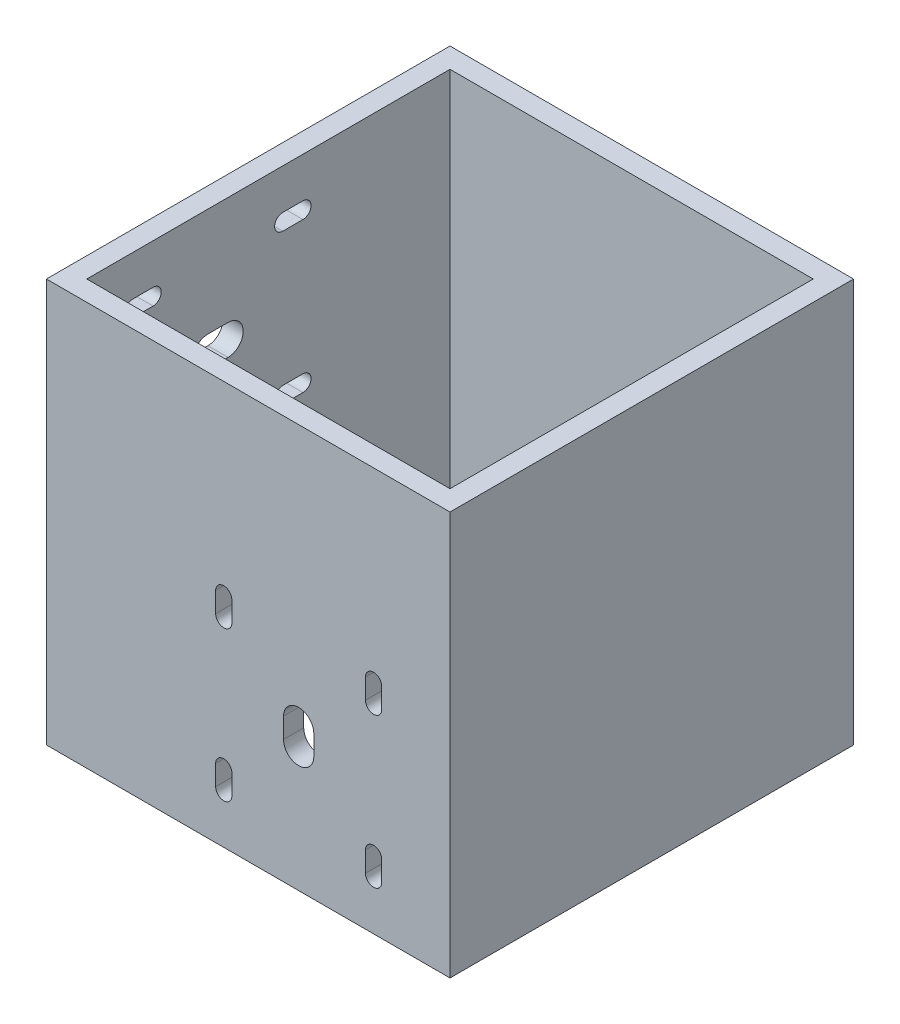
SolidWorks part; units mm, degrees
ref_plane "Front Plane" through (0, 0, 0) normal (0, 0, 1) x (1, 0, 0)
ref_plane "Top Plane" through (0, 0, 0) normal (0, 1, 0) x (1, 0, 0)
ref_plane "Right Plane" through (0, 0, 0) normal (1, 0, 0) x (0, 0, -1)
sketch "Sketch2" plane through (0, 0, 0) normal (0, 1, 0) x (1, 0, 0)
  line L0 (-57.15, 57.15) -> (57.15, 57.15)
  line L1 (-63.5, -63.5) -> (63.5, -63.5)
  line L2 (-63.5, -63.5) -> (-63.5, 63.5)
  line L3 (-63.5, 63.5) -> (63.5, 63.5)
  line L4 (63.5, -63.5) -> (63.5, 63.5)
  line L5 (-63.5, -63.5) -> (63.5, 63.5) construction
  line L6 (-63.5, 63.5) -> (63.5, -63.5) construction
  line L7 (57.15, -57.15) -> (57.15, 57.15)
  line L8 (-57.15, -57.15) -> (57.15, -57.15)
  line L9 (-57.15, -57.15) -> (-57.15, 57.15)
  point P0 (0, 0)
  dimension "D1" = 127
  dimension "D2" = 127
  dimension "D3" = 6.35
extrude "Boss-Extrude2" add sketch "Sketch2" along normal blind 127
sketch "Sketch3" plane through (0, 127, 0) normal (0, 1, 0) x (1, 0, 0)
  line L1 (57.15, 57.15) -> (-57.15, 57.15)
  line L2 (57.15, 57.15) -> (57.15, -57.15)
  line L3 (57.15, -57.15) -> (-57.15, -57.15)
  line L4 (-57.15, 57.15) -> (-57.15, -57.15)
  circle A0 centre (0, 0) radius 12.7
  dimension "D1" = 25.4
extrude "Boss-Extrude3" [suppressed] add sketch "Sketch3" against normal blind 6.35
sketch "Sketch6" plane through (-63.5, 0, 0) normal (-1, 0, 0) x (0, 0, 1)
  line L0 (-4.5232, 111.7473) -> (-10.8732, 111.7473) construction
  line L1 (-7.6982, 64.601) -> (39.4482, 64.601) construction
  line L2 (-7.6982, 64.601) -> (-7.6982, 111.7473) construction
  line L3 (-7.6982, 111.7473) -> (39.4482, 111.7473) construction
  line L4 (39.4482, 64.601) -> (39.4482, 111.7473) construction
  line L5 (-7.6982, 64.601) -> (39.4482, 111.7473) construction
  line L6 (-7.6982, 111.7473) -> (39.4482, 64.601) construction
  line L7 (-4.5232, 109.1946) -> (-10.8732, 109.1946)
  line L8 (-4.5232, 114.3) -> (-10.8732, 114.3)
  line L9 (36.2732, 111.7473) -> (42.6232, 111.7473) construction
  line L10 (36.2732, 114.3) -> (42.6232, 114.3)
  line L11 (36.2732, 109.1946) -> (42.6232, 109.1946)
  line L12 (36.2732, 64.601) -> (42.6232, 64.601) construction
  line L13 (36.2732, 67.1537) -> (42.6232, 67.1537)
  line L14 (36.2732, 62.0483) -> (42.6232, 62.0483)
  line L15 (-4.5232, 64.601) -> (-10.8732, 64.601) construction
  line L16 (-4.5232, 62.0483) -> (-10.8732, 62.0483)
  line L17 (-4.5232, 67.1537) -> (-10.8732, 67.1537)
  line L18 (-63.5, 127) -> (-63.5, 0) construction
  line L19 (-63.5, 127) -> (63.5, 127) construction
  line L20 (19.05, 88.1741) -> (12.7, 88.1741) construction
  line L21 (19.05, 83.4116) -> (12.7, 83.4116)
  line L22 (19.05, 92.9366) -> (12.7, 92.9366)
  circle A0 centre (15.875, 88.1741) radius 33.3375 construction
  arc A1 (-4.5232, 109.1946) -> (-4.5232, 114.3) centre (-4.5232, 111.7473) ccw
  arc A2 (-10.8732, 114.3) -> (-10.8732, 109.1946) centre (-10.8732, 111.7473) ccw
  arc A3 (36.2732, 114.3) -> (36.2732, 109.1946) centre (36.2732, 111.7473) ccw
  arc A4 (42.6232, 109.1946) -> (42.6232, 114.3) centre (42.6232, 111.7473) ccw
  arc A5 (36.2732, 67.1537) -> (36.2732, 62.0483) centre (36.2732, 64.601) ccw
  arc A6 (42.6232, 62.0483) -> (42.6232, 67.1537) centre (42.6232, 64.601) ccw
  arc A7 (-4.5232, 62.0483) -> (-4.5232, 67.1537) centre (-4.5232, 64.601) ccw
  arc A8 (-10.8732, 67.1537) -> (-10.8732, 62.0483) centre (-10.8732, 64.601) ccw
  arc A10 (19.05, 83.4116) -> (19.05, 92.9366) centre (19.05, 88.1741) ccw
  arc A11 (12.7, 92.9366) -> (12.7, 83.4116) centre (12.7, 88.1741) ccw
  point P8 (-7.6982, 111.7473)
  point P14 (39.4482, 111.7473)
  point P21 (39.4482, 64.601)
  point P28 (-7.6982, 64.601)
  point P41 (15.875, 88.1741)
  dimension "D3" = 6.35
  dimension "D1" = 66.675
  dimension "D6" = 2.5527
  dimension "D7" = 2.5527
  dimension "D8" = 2.5527
  dimension "D9" = 2.5527
  dimension "D14" = 4.7625
  dimension "D2" = 6.35
  dimension "D4" = 6.35
  dimension "D5" = 6.35
  dimension "D11" = 12.7
  dimension "D12" = 90
  dimension "D10" = 79.375
  dimension "D13" = 6.35
extrude "Cut-Extrude1" cut sketch "Sketch6" against normal up to next
sketch "Sketch8" plane through (0, 0, 63.5) normal (0, 0, 1) x (1, 0, 0)
  line L0 (-7.6982, 62.399) -> (-7.6982, 68.749) construction
  line L1 (-7.6982, 18.4277) -> (39.4482, 18.4277) construction
  line L2 (-7.6982, 18.4277) -> (-7.6982, 65.574) construction
  line L3 (-7.6982, 65.574) -> (39.4482, 65.574) construction
  line L4 (39.4482, 18.4277) -> (39.4482, 65.574) construction
  line L5 (-7.6982, 18.4277) -> (39.4482, 65.574) construction
  line L6 (-7.6982, 65.574) -> (39.4482, 18.4277) construction
  line L7 (-10.2509, 62.399) -> (-10.2509, 68.749)
  line L8 (-5.1455, 62.399) -> (-5.1455, 68.749)
  line L9 (39.4482, 62.399) -> (39.4482, 68.749) construction
  line L10 (36.8955, 62.399) -> (36.8955, 68.749)
  line L11 (42.0009, 62.399) -> (42.0009, 68.749)
  line L12 (39.4482, 21.6027) -> (39.4482, 15.2527) construction
  line L13 (42.0009, 21.6027) -> (42.0009, 15.2527)
  line L14 (36.8955, 21.6027) -> (36.8955, 15.2527)
  line L15 (-7.6982, 15.2527) -> (-7.6982, 21.6027) construction
  line L16 (-10.2509, 15.2527) -> (-10.2509, 21.6027)
  line L17 (-5.1455, 15.2527) -> (-5.1455, 21.6027)
  line L18 (-63.5, 127) -> (-63.5, 0) construction
  line L19 (-63.5, 0) -> (63.5, 0) construction
  line L20 (15.875, 38.8259) -> (15.875, 45.1759) construction
  line L21 (11.1125, 38.8259) -> (11.1125, 45.1759)
  line L22 (20.6375, 38.8259) -> (20.6375, 45.1759)
  circle A0 centre (15.875, 42.0009) radius 33.3375 construction
  arc A1 (-10.2509, 62.399) -> (-5.1455, 62.399) centre (-7.6982, 62.399) ccw
  arc A2 (-5.1455, 68.749) -> (-10.2509, 68.749) centre (-7.6982, 68.749) ccw
  arc A3 (36.8955, 62.399) -> (42.0009, 62.399) centre (39.4482, 62.399) ccw
  arc A4 (42.0009, 68.749) -> (36.8955, 68.749) centre (39.4482, 68.749) ccw
  arc A5 (42.0009, 21.6027) -> (36.8955, 21.6027) centre (39.4482, 21.6027) ccw
  arc A6 (36.8955, 15.2527) -> (42.0009, 15.2527) centre (39.4482, 15.2527) ccw
  arc A7 (-10.2509, 15.2527) -> (-5.1455, 15.2527) centre (-7.6982, 15.2527) ccw
  arc A8 (-5.1455, 21.6027) -> (-10.2509, 21.6027) centre (-7.6982, 21.6027) ccw
  arc A9 (11.1125, 38.8259) -> (20.6375, 38.8259) centre (15.875, 38.8259) ccw
  arc A10 (20.6375, 45.1759) -> (11.1125, 45.1759) centre (15.875, 45.1759) ccw
  point P8 (-7.6982, 65.574)
  point P15 (39.4482, 65.574)
  point P22 (39.4482, 18.4277)
  point P29 (-7.6982, 18.4277)
  point P37 (-7.6982, 12.7)
  point P41 (15.875, 42.0009)
  dimension "D7" = 66.675
  dimension "D12" = 2.5527
  dimension "D13" = 2.5527
  dimension "D14" = 2.5527
  dimension "D15" = 2.5527
  dimension "D18" = 4.7625
  dimension "D1" = 90
  dimension "D2" = 90
  dimension "D3" = 90
  dimension "D4" = 90
  dimension "D5" = 90
  dimension "D6" = 79.375
  dimension "D9" = 6.35
  dimension "D8" = 6.35
  dimension "D10" = 6.35
  dimension "D11" = 6.35
  dimension "D16" = 12.7
  dimension "D17" = 6.35
extrude "Cut-Extrude2" cut sketch "Sketch8" against normal up to next
equation "\"BoxSize\" = 5in'Size of the exterior of the box. Take half this to put stuff on midpoint."
equation "\"D2@Sketch2\"=\"BoxSize\""
equation "\"D1@Sketch2\"=\"BoxSize\""
equation "\"D10@Sketch6\"=(\"WormPitchDiameter\"+\"WormGearPitchDiameter\"+\"BoxSize\")/2"
equation "\"SlotLengthRadius\"= .25in'Length of slots to align motors. Keep small."
equation "\"D2@Sketch6\"=\"SlotLengthRadius\""
equation "\"D3@Sketch6\"=\"SlotLengthRadius\""
equation "\"D5@Sketch6\"=\"SlotLengthRadius\""
equation "\"D4@Sketch6\"=\"SlotLengthRadius\""
equation "\"D13@Sketch6\"=\"SlotLengthRadius\""
equation "\"WormPitchDiameter\"= 0.25in"
equation "\"WormGearPitchDiameter\"= 1in"
equation "\"D6@Sketch8\"=(\"BoxSize\"+\"WormPitchDiameter\"+\"WormGearPitchDiameter\")/2"
equation "\"D9@Sketch8\"=\"SlotLengthRadius\""
equation "\"D8@Sketch8\"=\"SlotLengthRadius\""
equation "\"D10@Sketch8\"=\"SlotLengthRadius\""
equation "\"D11@Sketch8\"=\"SlotLengthRadius\""
